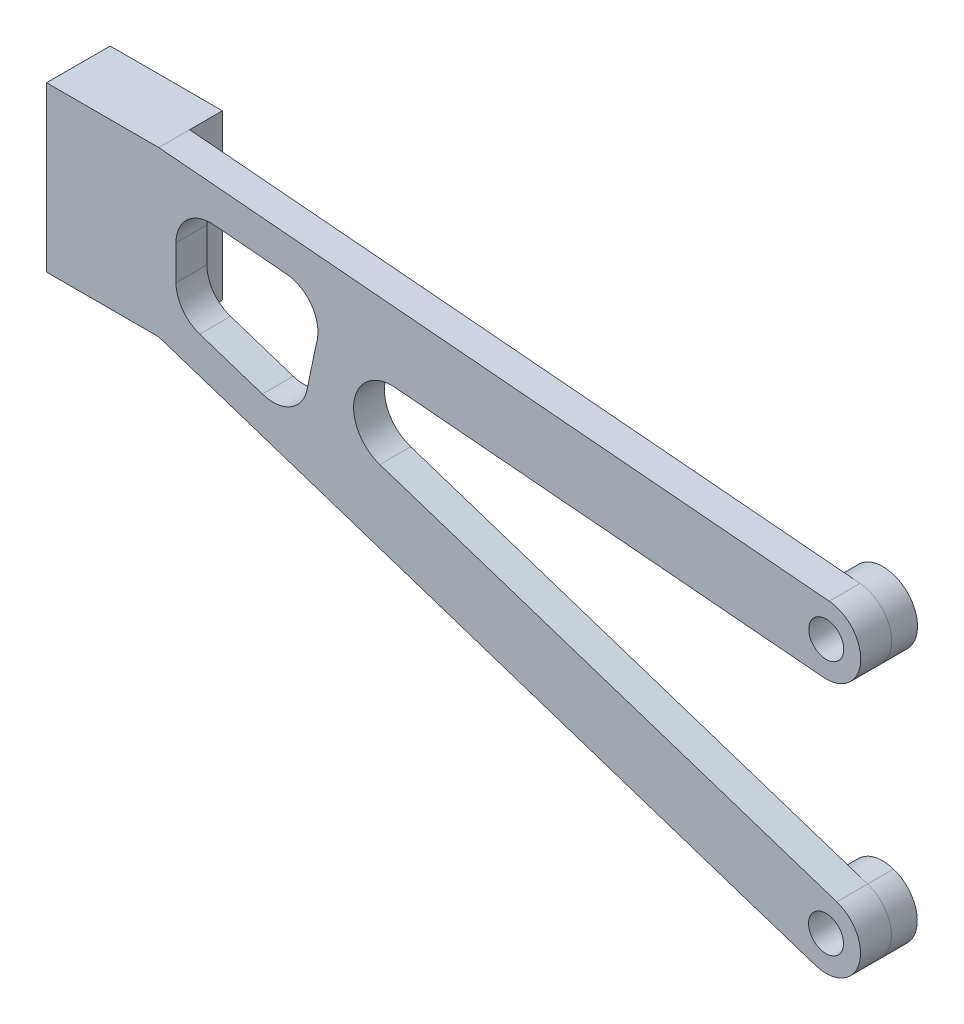
SolidWorks part; units mm, degrees
ref_plane "Front Plane" through (0, 0, 0) normal (0, 0, 1) x (1, 0, 0)
ref_plane "Top Plane" through (0, 0, 0) normal (0, 1, 0) x (1, 0, 0)
ref_plane "Right Plane" through (0, 0, 0) normal (1, 0, 0) x (0, 0, -1)
sketch "Sketch2" plane through (0, 0, 0) normal (0, 0, 1) x (1, 0, 0)
  line L0 (0, 19) -> (0, 0)
  line L1 (0, 0) -> (13, 0)
  line L2 (13, 0) -> (89.0605, -25.0081)
  line L4 (91.5592, -17.4083) -> (38.6172, -0.0014)
  line L9 (40.3795, 8.615) -> (89.9923, 4.3468)
  line L10 (0, 19) -> (13, 19)
  line L11 (13, 19) -> (90.678, 12.3174)
  line L12 (90.3225, -6.438) -> (40, 4.2042) construction
  line L14 (15, 10.4543) -> (15, 6.4486)
  line L15 (17.7506, 2.6487) -> (24.9974, 0.266)
  line L16 (30.1602, 3.2383) -> (31.3576, 8.9002)
  line L17 (27.787, 13.7131) -> (19.3429, 14.4396)
  line L18 (90.3351, 8.3321) -> (90.3099, -21.2082) construction
  circle A0 centre (90.3351, 8.3321) radius 2.025
  circle A1 centre (90.3099, -21.2082) radius 2.025
  arc A2 (90.678, 12.3174) -> (89.9923, 4.3468) centre (90.3351, 8.3321) cw
  arc A3 (91.5592, -17.4083) -> (89.0605, -25.0081) centre (90.3099, -21.2082) cw
  arc A4 (40.3795, 8.615) -> (38.6172, -0.0014) centre (40, 4.2042) ccw
  arc A5 (24.9974, 0.266) -> (30.1602, 3.2383) centre (26.2468, 4.0659) ccw
  arc A6 (31.3576, 8.9002) -> (27.787, 13.7131) centre (27.4442, 9.7278) ccw
  arc A7 (15, 10.4543) -> (19.3429, 14.4396) centre (19, 10.4543) cw
  arc A8 (15, 6.4486) -> (17.7506, 2.6487) centre (19, 6.4486) ccw
  point P6 (0, 0)
  point P9 (35.6627, 5.0913)
  dimension "D6" = 4.05
  dimension "D7" = 4.05
  dimension "D17" = 4
  dimension "D1" = 8
  dimension "D2" = 8
  dimension "D3" = 19
  dimension "D4" = 13
  dimension "D5" = 13
  dimension "D8" = 40
  dimension "D9" = 21.2082
  dimension "D10" = 90.3099
  dimension "D11" = 8.3321
  dimension "D12" = 90.3351
  dimension "D13" = 4
  dimension "D14" = 4
  dimension "D15" = 15
  dimension "D16" = 5
extrude "Boss-Extrude1" add sketch "Sketch2" along normal blind 6.575
sketch "Sketch3" plane through (0, 0, 0) normal (0, 0, -1) x (-1, 0, 0)
  line L1 (-13, 19) -> (-98, 19)
  line L2 (-13, 19) -> (-13, -26)
  line L3 (-13, -26) -> (-98, -26)
  line L4 (-98, 19) -> (-98, -26)
  circle A0 centre (-90.3351, 8.3321) radius 4
  circle A1 centre (-90.3096, -21.2081) radius 4
  dimension "D3" = 8
  dimension "D4" = 8
  dimension "D1" = 45
  dimension "D2" = 85
extrude "Cut-Extrude1" cut sketch "Sketch3" against normal blind 3
sketch "Sketch4" plane through (0, 0, 0) normal (0, 0, -1) x (-1, 0, 0)
  line L0 (0, 19) -> (-13, 19)
  line L1 (-13, 19) -> (0, 19) construction
  line L2 (-13, 19) -> (-13, 0)
  line L3 (0, 0) -> (-13, 0) construction
  line L4 (-13, 0) -> (-89.0602, -25.008) construction
  line L5 (-13, 0) -> (-10.5, 0)
  line L6 (-10.5, 0) -> (-10.5, 16.5)
  line L7 (-10.5, 16.5) -> (0, 16.5)
  line L8 (0, 19) -> (0, 0) construction
  line L9 (0, 16.5) -> (0, 19)
  dimension "D1" = 2.5
  dimension "D2" = 2.5
extrude "Boss-Extrude2" add sketch "Sketch4" along normal blind 0.8
